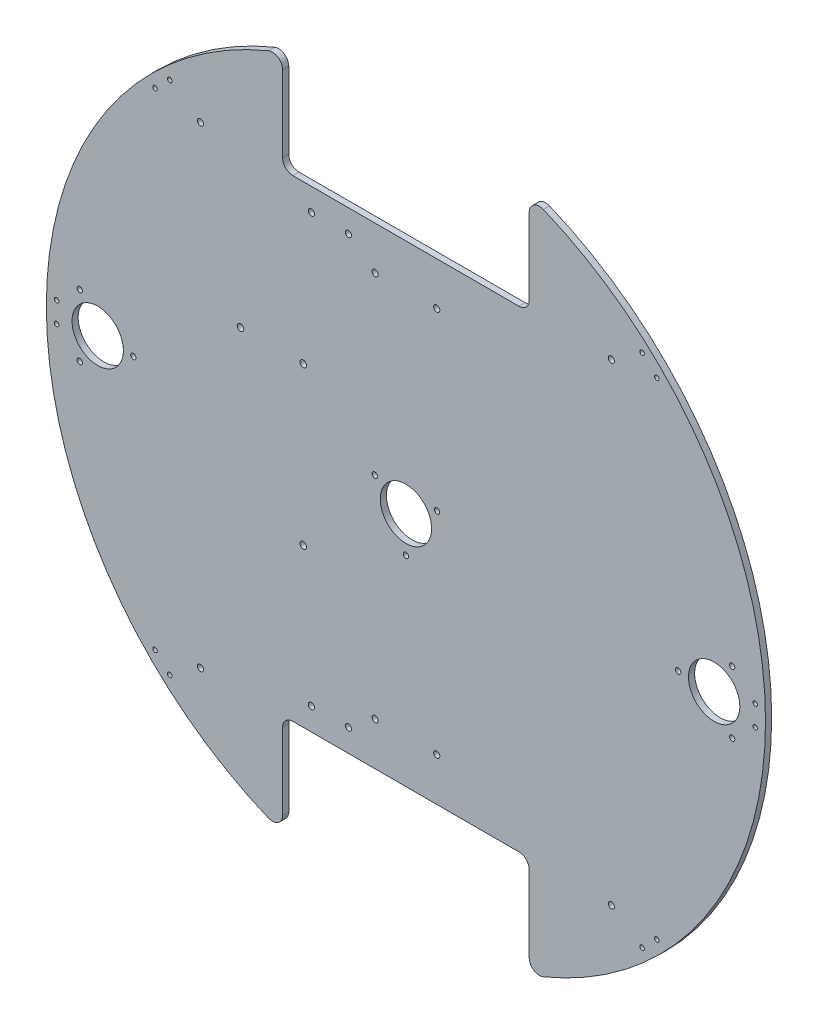
SolidWorks part; units mm, degrees
material "ｱｸﾘﾙ (中-上級の耐衝撃性)"
ref_plane "正面" through (0, 0, 0) normal (0, 0, 1) x (1, 0, 0)
ref_plane "平面" through (0, 0, 0) normal (0, 1, 0) x (1, 0, 0)
ref_plane "右側面" through (0, 0, 0) normal (1, 0, 0) x (0, 0, -1)
sketch "ｽｹｯﾁ1" plane through (0, 0, 0) normal (0, 0, 1) x (1, 0, 0)
  circle A0 centre (0, 0) radius 175
  dimension "D1" = 350
extrude "ﾎﾞｽ - 押し出し1" add sketch "ｽｹｯﾁ1" along normal blind 3
sketch "ｽｹｯﾁ2" plane through (0, 0, 3) normal (0, 0, 1) x (1, 0, 0)
  line L0 (0, 0) -> (175, 0)
  line L1 (0, 0) -> (-175, 0)
  line L2 (0, 0) -> (0, 115)
  line L3 (0, 0) -> (0, -115)
  line L4 (0, 115) -> (60, 115)
  line L5 (0, 115) -> (0, 175)
  line L6 (0, 175) -> (60, 175)
  line L7 (60, 115) -> (60, 175)
  line L8 (0, 115) -> (-60, 115)
  line L9 (0, 115) -> (0, 175)
  line L10 (0, 175) -> (-60, 175)
  line L11 (-60, 115) -> (-60, 175)
  line L13 (0, -115) -> (60, -115)
  line L14 (0, -115) -> (0, -175)
  line L15 (0, -175) -> (60, -175)
  line L16 (60, -115) -> (60, -175)
  line L17 (0, -115) -> (-60, -115)
  line L18 (0, -115) -> (0, -175)
  line L19 (0, -175) -> (-60, -175)
  line L20 (-60, -115) -> (-60, -175)
  circle A0 centre (0, 0) radius 175 construction
  circle M1 centre (0, 0) radius 175
  dimension "D1" = 115
  dimension "D2" = 60
  dimension "D3" = 60
  dimension "D4" = 60
  dimension "D5" = 115
  dimension "D6" = 60
extrude "ｶｯﾄ - 押し出し1" cut sketch "ｽｹｯﾁ2" against normal blind 3 contours L11 L8 L5 M1 | L4 L7 L5 M1 | L17 L20 L14 M1 | L16 L13 L14 M1
fillet "ﾌｨﾚｯﾄ1" radius 5 1 edges at (-60, 164.3928, 1.5)
fillet "ﾌｨﾚｯﾄ2" radius 5 3 edges at (60, 115, 1.5) (60, 164.3928, 1.5) (-60, 115, 1.5)
fillet "ﾌｨﾚｯﾄ3" radius 5 4 edges at (-60, -164.3928, 1.5) (-60, -115, 1.5) (60, -164.3928, 1.5) (60, -115, 1.5)
sketch "ｽｹｯﾁ5" plane through (0, 0, 3) normal (0, 0, 1) x (1, 0, 0)
  line L0 (0, 115) -> (-100, 115)
  line L1 (55, 115) -> (-55, 115) construction
  line L2 (0, 115) -> (100, 115)
  line L3 (0, -115) -> (100, -115)
  line L4 (55, -115) -> (-55, -115) construction
  line L5 (100, -115) -> (-100, -115)
  circle A0 centre (-100, -115) radius 1.5
  circle A1 centre (100, -115) radius 1.5
  circle A2 centre (100, 115) radius 1.5
  circle A3 centre (-100, 115) radius 1.5
  dimension "D3" = 3
  dimension "D4" = 3
  dimension "D5" = 3
  dimension "D6" = 3
  dimension "D1" = 100
  dimension "D2" = 100
extrude "ｶｯﾄ - 押し出し4" cut sketch "ｽｹｯﾁ5" against normal blind 3 contours A1 | A0 | A3 | A2
sketch "ｽｹｯﾁ10" plane through (0, 0, 3) normal (0, 0, 1) x (1, 0, 0)
  line L0 (0, 0) -> (-150, 0)
  line L1 (0, 0) -> (150, 0)
  line L2 (-150, 0) -> (-158.75, 15.1554)
  line L3 (-150, 0) -> (-158.75, -15.1554)
  line L4 (-150, 0) -> (-132.6329, 0)
  line L5 (0, 0) -> (15.1554, 8.75)
  line L6 (0, 0) -> (-15.1554, 8.75)
  line L7 (0, 0) -> (0, -17.5)
  line L8 (150, 0) -> (158.75, 15.1554)
  line L9 (150, 0) -> (132.5, 0)
  line L10 (150, 0) -> (158.75, -15.1554)
  circle A0 centre (-150, 0) radius 12.5
  circle A1 centre (150, 0) radius 12.5
  circle A2 centre (0, 0) radius 12.5
  circle A3 centre (-150, 0) radius 17.5
  circle A4 centre (0, 0) radius 17.5
  circle A5 centre (150, 0) radius 17.5
  circle A6 centre (132.5, 0) radius 1.3
  circle A7 centre (158.75, 15.1554) radius 1.3
  circle A8 centre (158.75, -15.1554) radius 1.3
  circle A9 centre (-15.1554, 8.75) radius 1.3
  circle A10 centre (15.1554, 8.75) radius 1.3
  circle A11 centre (0, -17.5) radius 1.3
  circle A12 centre (-158.75, 15.1554) radius 1.3
  circle A13 centre (-158.75, -15.1554) radius 1.3
  circle A14 centre (-132.6329, 0) radius 1.3
  dimension "D3" = 25
  dimension "D4" = 25
  dimension "D5" = 25
  dimension "D6" = 35
  dimension "D7" = 35
  dimension "D8" = 35
  dimension "D15" = 2.6
  dimension "D16" = 2.6
  dimension "D17" = 2.6
  dimension "D18" = 2.6
  dimension "D19" = 2.6
  dimension "D20" = 2.6
  dimension "D21" = 2.6
  dimension "D22" = 2.6
  dimension "D23" = 2.6
  dimension "D1" = 150
  dimension "D2" = 150
  dimension "D9" = 120
  dimension "D10" = 120
  dimension "D11" = 120
  dimension "D12" = 120
  dimension "D13" = 120
  dimension "D14" = 120
sketch "ｽｹｯﾁ12" plane through (0, 0, 3) normal (0, 0, 1) x (1, 0, 0)
  line L0 (0, 115) -> (0, 94)
  line L1 (55, 115) -> (-55, 115) construction
  line L2 (0, 94) -> (15, 94)
  line L3 (0, 94) -> (-15, 94)
  line L7 (0, -115) -> (0, -94)
  line L8 (55, -115) -> (-55, -115) construction
  line L9 (0, -94) -> (15, -94)
  line L10 (0, -94) -> (-15, -94)
  circle A0 centre (-15, 94) radius 1.5
  circle A1 centre (15, 94) radius 1.5
  circle A6 centre (-15, -94) radius 1.5
  circle A7 centre (15, -94) radius 1.5
  dimension "D5" = 3
  dimension "D6" = 3
  dimension "D7" = 15
  dimension "D13" = 3
  dimension "D14" = 3
  dimension "D1" = 21
  dimension "D2" = 15
  dimension "D3" = 15
  dimension "D4" = 15
  dimension "D9" = 21
sketch "ｽｹｯﾁ13" plane through (0, 0, 3) normal (0, 0, 1) x (1, 0, 0)
  line L0 (0, -115) -> (-25, -115)
  line L1 (55, -115) -> (-55, -115) construction
  line L2 (-25, -115) -> (-25, -104)
  line L3 (-46, 104) -> (-28, 104)
  line L4 (0, 115) -> (-28, 115)
  line L5 (-28, -104) -> (-46, -104)
  line L6 (-28, 104) -> (-27.8272, 103.8289)
  line L7 (0, 115) -> (0, -115)
  line L9 (55, 115) -> (-55, 115) construction
  line L10 (-28, 115) -> (-28, 104)
  line L12 (-28, 104) -> (-46, 104)
  circle A1 centre (-28, -104) radius 1.5
  circle A2 centre (-46, -104) radius 1.5
  circle A4 centre (-46, 104) radius 1.5
  circle A7 centre (-28, 104) radius 1.5
  dimension "D8" = 3
  dimension "D9" = 3
  dimension "D13" = 3
  dimension "D14" = 3
  dimension "D1" = 25
  dimension "D2" = 11
  dimension "D3" = 3
  dimension "D4" = 18
  dimension "D5" = 18
  dimension "D10" = 28
  dimension "D11" = 11
extrude "ｶｯﾄ - 押し出し13" cut sketch "ｽｹｯﾁ10" against normal blind 10 contours A12 | A0 | A13 | A14 | A2 | A9 | A10 | A11 | A6 | A1 | A7 | A8
sketch "ｽｹｯﾁ14" plane through (0, 0, 3) normal (0, 0, 1) x (1, 0, 0)
  line L0 (0, 0) -> (-170, 0)
  line L1 (-170, 0) -> (-170, 5)
  line L2 (-170, 0) -> (-170, -5)
  line L3 (0, 0) -> (-118.5181, 121.8748)
  line L4 (0, 0) -> (-118.5181, -121.8748)
  line L5 (-118.5181, 121.8748) -> (-114.9335, 125.3606)
  line L6 (-118.5181, 121.8748) -> (-122.1026, 118.389)
  line L7 (-118.5181, -121.8748) -> (-122.1026, -118.389)
  line L8 (-118.5181, -121.8748) -> (-114.9335, -125.3606)
  circle A0 centre (-170, 5) radius 1.1
  circle A1 centre (-170, -5) radius 1.1
  circle A2 centre (-114.9335, 125.3606) radius 1.1
  circle A3 centre (-122.1026, 118.389) radius 1.1
  circle A4 centre (-122.1026, -118.389) radius 1.1
  circle A5 centre (-114.9335, -125.3606) radius 1.1
  dimension "D4" = 2.2
  dimension "D5" = 2.2
  dimension "D14" = 2.2
  dimension "D15" = 2.2
  dimension "D16" = 2.2
  dimension "D17" = 2.2
  dimension "D1" = 170
  dimension "D2" = 5
  dimension "D3" = 5
  dimension "D6" = 45.8
  dimension "D7" = 45.8
  dimension "D8" = 170
  dimension "D9" = 170
  dimension "D10" = 5
  dimension "D11" = 5
  dimension "D12" = 5
  dimension "D13" = 5
extrude "ｶｯﾄ - 押し出し14" cut sketch "ｽｹｯﾁ14" against normal blind 10 contours A4 | A5 | A0 | A1 | A2 | A3
extrude "ｶｯﾄ - 押し出し17" cut sketch "ｽｹｯﾁ12" against normal blind 10 contours A6 | A7 | A0 | A1
extrude "ｶｯﾄ - 押し出し18" cut sketch "ｽｹｯﾁ13" against normal blind 5 contours A2 | A1 | A4 | A7
sketch "ｽｹｯﾁ17" plane through (0, 0, 3) normal (0, 0, 1) x (1, 0, 0)
  line L0 (0, 0) -> (208.059, 0)
  line L1 (208.059, 0) -> (0, 0)
  line L2 (0, 0) -> (138.4473, 142.3685)
  line L3 (138.4473, 142.3685) -> (0, 0)
  line L4 (0, 0) -> (137.4586, -141.3518)
  line L5 (137.4586, -141.3518) -> (0, 0)
  line L6 (0, 0) -> (-17.446, 16.9654)
  line L7 (-17.446, 16.9654) -> (0, 0)
  line L8 (0, 0) -> (-16.1459, -15.7012)
  line L9 (-16.1459, -15.7012) -> (0, 0)
  circle A0 centre (170, 5) radius 1.1
  circle A1 centre (170, -5) radius 1.1
  circle A2 centre (114.9335, 125.3606) radius 1.1
  circle A3 centre (122.1026, 118.389) radius 1.1
  circle A4 centre (122.1026, -118.389) radius 1.1
  circle A5 centre (114.9335, -125.3606) radius 1.1
  dimension "D5" = 2.2
  dimension "D6" = 2.2
  dimension "D13" = 2.2
  dimension "D14" = 2.2
  dimension "D19" = 2.2
  dimension "D20" = 2.2
  dimension "D1" = 45.8
  dimension "D2" = 45.8
  dimension "D3" = 5
  dimension "D4" = 5
  dimension "D7" = 170
  dimension "D8" = 170
  dimension "D9" = 90
  dimension "D10" = 90
  dimension "D11" = 5
  dimension "D12" = 5
  dimension "D15" = 170
  dimension "D16" = 170
  dimension "D17" = 5
  dimension "D18" = 5
  dimension "D21" = 170
  dimension "D22" = 170
extrude "ｶｯﾄ - 押し出し19" cut sketch "ｽｹｯﾁ17" against normal blind 10 contours A2 | A3 | A0 | A1 | A4 | A5
sketch "ｽｹｯﾁ18" plane through (0, 0, 3) normal (0, 0, 1) x (1, 0, 0)
  line L0 (0, 0) -> (-119.2427, 0)
  line L1 (-119.2427, 0) -> (0, 0)
  circle A0 centre (-50, 38.25) radius 1.6
  circle A1 centre (-80.5, 38.25) radius 1.6
  circle A2 centre (-50, -38.25) radius 1.6
  dimension "D7" = 3.2
  dimension "D8" = 3.2
  dimension "D9" = 3.2
  dimension "D1" = 38.25
  dimension "D2" = 38.25
  dimension "D3" = 38.25
  dimension "D4" = 30.5
  dimension "D5" = 50
  dimension "D6" = 50
extrude "ｶｯﾄ - 押し出し20" cut sketch "ｽｹｯﾁ18" against normal blind 10 contours A1 | A0 | A2
